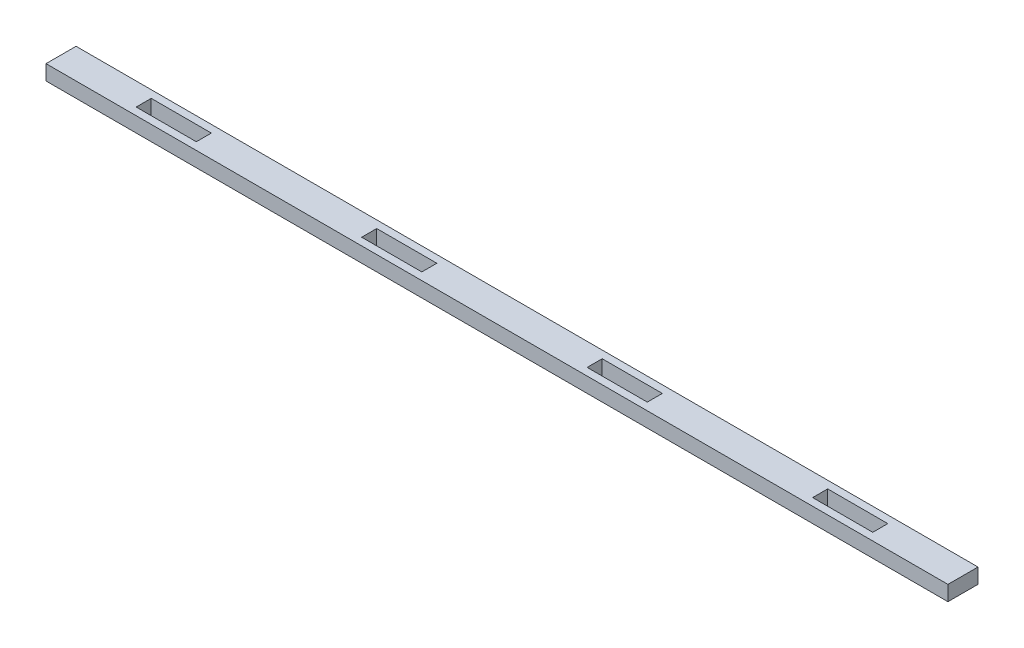
SolidWorks part; units mm, degrees
material "Cedar"
ref_plane "Front Plane" through (0, 0, 0) normal (0, 0, 1) x (1, 0, 0)
ref_plane "Top Plane" through (0, 0, 0) normal (0, 1, 0) x (1, 0, 0)
ref_plane "Right Plane" through (0, 0, 0) normal (1, 0, 0) x (0, 0, -1)
sketch "Sketch1" plane through (0, 0, 0) normal (0, 1, 0) x (1, 0, 0)
  line L1 (-190.5, 6.35) -> (190.5, 6.35)
  line L2 (-190.5, 6.35) -> (-190.5, -6.35)
  line L3 (-190.5, -6.35) -> (190.5, -6.35)
  line L4 (190.5, 6.35) -> (190.5, -6.35)
  line L5 (-190.5, 6.35) -> (190.5, -6.35) construction
  line L6 (-190.5, -6.35) -> (190.5, 6.35) construction
  point P0 (0, 0)
  dimension "D1" = 381
  dimension "D2" = 12.7
extrude "Boss-Extrude1" add sketch "Sketch1" along normal blind 6.35
sketch "Sketch2" plane through (0, 6.35, 0) normal (0, 1, 0) x (1, 0, 0)
  line L0 (-190.5, 0) -> (-155.575, 0) construction
  line L1 (-155.575, 3.175) -> (-130.175, 3.175)
  line L2 (-155.575, 3.175) -> (-155.575, -3.175)
  line L3 (-155.575, -3.175) -> (-130.175, -3.175)
  line L4 (-130.175, 3.175) -> (-130.175, -3.175)
  line L5 (-155.575, 3.175) -> (-130.175, -3.175) construction
  line L6 (-155.575, -3.175) -> (-130.175, 3.175) construction
  line L7 (-190.5, 6.35) -> (-190.5, -6.35) construction
  point P0 (-142.875, 0)
  dimension "D1" = 25.4
  dimension "D2" = 6.35
  dimension "D3" = 34.925
extrude "Cut-Extrude1" cut sketch "Sketch2" against normal through all
pattern_linear "LPattern1" count 4 spacing 95.25 along (1, 0, 0) of "Cut-Extrude1"
